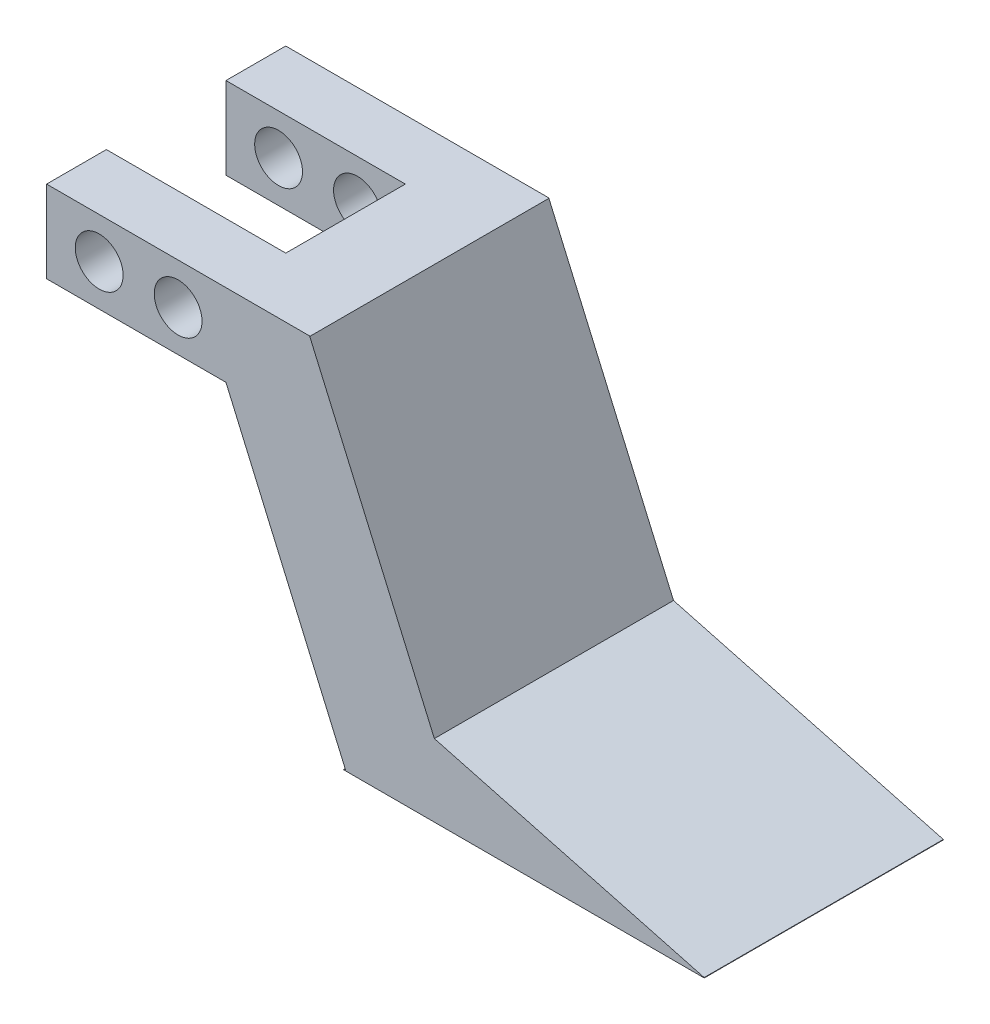
SolidWorks part; units mm, degrees
ref_plane "Front Plane" through (0, 0, 0) normal (0, 0, 1) x (1, 0, 0)
ref_plane "Top Plane" through (0, 0, 0) normal (0, 1, 0) x (1, 0, 0)
ref_plane "Right Plane" through (0, 0, 0) normal (1, 0, 0) x (0, 0, -1)
sketch "Sketch2" plane through (0, 0, 0) normal (0, 0, 1) x (1, 0, 0)
  line L1 (-0.0745, 0.149) -> (14.9255, 0.149)
  line L2 (-0.0745, 0.149) -> (-0.0745, 7.009)
  line L3 (-0.0745, 7.009) -> (14.9255, 7.009)
  line L4 (14.9255, 0.149) -> (14.9255, 7.009)
  dimension "D1" = 15
  dimension "D2" = 6.86
extrude "Boss-Extrude1" add sketch "Sketch2" along normal blind 20
sketch "Sketch4" plane through (0, 0, 20) normal (0, 0, 1) x (1, 0, 0)
  line L0 (14.9255, 0.149) -> (14.9255, 7.009) construction
  line L1 (14.9255, 7.009) -> (54.9255, 7.009)
  line L2 (14.9255, 7.009) -> (14.9255, -22.991)
  line L3 (14.9255, -22.991) -> (54.9255, -22.991)
  line L4 (54.9255, 7.009) -> (54.9255, -22.991)
  line L5 (14.9255, 7.009) -> (-0.0745, 7.009) construction
  dimension "D1" = 0
  dimension "D2" = 0
  dimension "D3" = 40
  dimension "D4" = 30
extrude "Boss-Extrude2" add sketch "Sketch4" against normal blind 20
sketch "Sketch6" plane through (0, 0, 20) normal (0, 0, 1) x (1, 0, 0)
  line L0 (14.9255, 0.149) -> (24.9255, -22.9151)
  line L2 (14.9255, 0.149) -> (14.9255, -22.991)
  line L3 (14.9367, -22.991) -> (24.9367, -22.991)
  line L4 (14.9255, 0.149) -> (14.9255, -22.991) construction
  line L6 (14.9255, -22.991) -> (54.9255, -22.991) construction
  dimension "D1" = 10
  dimension "D2" = 30
  dimension "D3" = 23.14
  dimension "D4" = 0
  dimension "D5" = 0
  dimension "D6" = 0
extrude "Cut-Extrude-Thin1" cut sketch "Sketch6" against normal blind 20 thin
sketch "Sketch7" plane through (0, 0, 20) normal (0, 0, 1) x (1, 0, 0)
  line L0 (21.9272, 6.9941) -> (32.354, -16.9365)
  line L1 (32.354, -16.9365) -> (54.9741, -22.9761)
  line L2 (22.0411, 7.165) -> (54.9741, 6.9941)
  line L3 (54.9741, 6.9941) -> (54.9171, -22.9761)
extrude "Cut-Extrude-Thin2" cut sketch "Sketch7" against normal blind 20 thin thin type one direction reverse wall 10
sketch "Sketch10" plane through (0, 7.009, 0) normal (0, 1, 0) x (1, 0, 0)
  line L0 (-0.0745, -20) -> (-0.0745, 0) construction
  line L1 (-0.0745, -5) -> (14.9255, -5)
  line L2 (-0.0745, -5) -> (-0.0745, -15)
  line L3 (-0.0745, -15) -> (14.9255, -15)
  line L4 (14.9255, -5) -> (14.9255, -15)
  line L5 (21.9614, 0) -> (-0.0745, 0) construction
  line L6 (21.9614, -20) -> (-0.0745, -20) construction
  dimension "D1" = 15
  dimension "D2" = 0
  dimension "D3" = 5
  dimension "D4" = 5
extrude "Cut-Extrude4" cut sketch "Sketch10" against normal blind 20
sketch "Sketch11" plane through (0, 0, 20) normal (0, 0, 1) x (1, 0, 0)
  line L0 (-0.0745, 3.579) -> (14.9255, 3.579)
  line L1 (-0.0745, 0.149) -> (14.9255, 0.149) construction
  line L2 (-0.0745, 7.009) -> (-0.0745, 0.149) construction
  circle A0 centre (4.3255, 3.6006) radius 2
  circle A1 centre (10.9255, 3.5742) radius 2
  dimension "D3" = 4
  dimension "D4" = 4
  dimension "D1" = 15
  dimension "D2" = 3.43
  dimension "D5" = 4.4
  dimension "D6" = 6.6
  dimension "D7" = 4
extrude "Cut-Extrude5" cut sketch "Sketch11" against normal blind 20 contours L0 A0 | L0 A0 | L0 A1 | L0 A1
